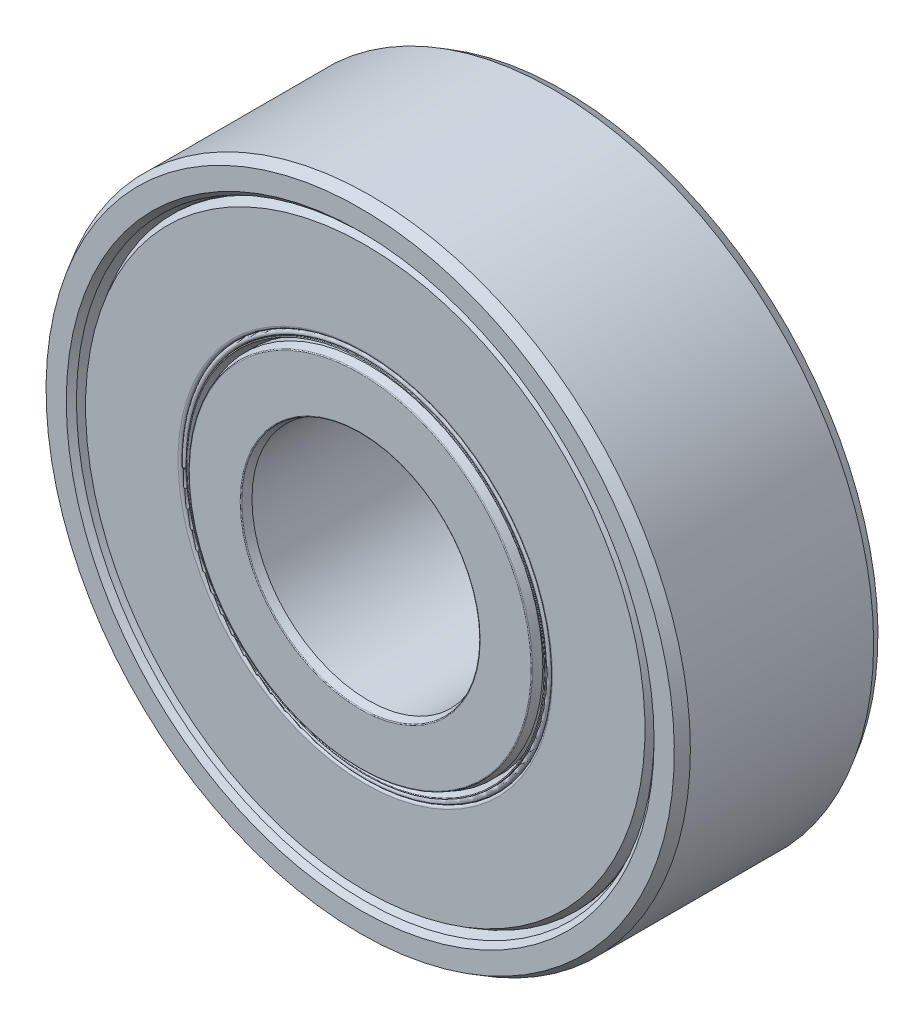
SolidWorks part; units mm, degrees
ref_plane "Front Plane" through (0, 0, 0) normal (0, 0, 1) x (1, 0, 0)
ref_plane "Top Plane" through (0, 0, 0) normal (0, 1, 0) x (1, 0, 0)
ref_plane "Right Plane" through (0, 0, 0) normal (1, 0, 0) x (0, 0, -1)
sketch "Sketch1" plane through (0, 0, 0) normal (0, 0, 1) x (1, 0, 0)
  line L0 (-11, 0) -> (11, 0) construction
  line L1 (-4, 0) -> (4, 0) construction
  circle A0 centre (0, 0) radius 4 construction
  circle A1 centre (0, 0) radius 11 construction
  point P3 (0, 0)
  point P6 (0, 0)
  point P7 (0, -4)
  point P11 (0, -11)
  point P12 (0, 4)
  point P13 (0, 11)
  dimension "OD" = 22
  dimension "ID" = 8
sketch "Sketch2" plane through (0, 0, 0) normal (1, 0, 0) x (0, 0, -1)
  line L0 (-3.5, 11) -> (3.5, 11) construction
  line L1 (0, 11) -> (0, -11) construction
  line L2 (3.15, 11) -> (-3.15, 11)
  line L3 (-3.15, 11) -> (-3.5, 10.7979)
  line L4 (-3.5, 10.7979) -> (-3.5, 10.1032)
  line L5 (-2.9452, 9.79) -> (-1.631, 9.79)
  line L6 (2.9452, 9.79) -> (1.631, 9.79)
  line L7 (3.5, 10.7979) -> (3.5, 10.1032)
  line L8 (3.15, 11) -> (3.5, 10.7979)
  line L9 (-1.631, 9.79) -> (-1.631, 11) construction
  line L10 (-1.631, 10.395) -> (0, 10.395) construction
  line L11 (0, 11) -> (0, -11) construction
  line L12 (-3.5, 0) -> (3.5, 0) construction
  line L13 (3.5, 4) -> (-3.5, 4) construction
  line L14 (-3.5, 4) -> (-3.5, -4) construction
  line L15 (-3.5, -4) -> (3.5, -4) construction
  line L16 (3.5, 11) -> (3.5, -11) construction
  line L20 (-2.9452, 9.79) -> (-3.325, 9.9282)
  line L21 (-3.325, 9.9282) -> (-3.5, 10.1032)
  line L26 (3.325, 9.9282) -> (3.5, 10.1032)
  line L27 (2.9452, 9.79) -> (3.325, 9.9282)
  arc A0 (-1.631, 9.79) -> (1.631, 9.79) centre (0, 7.894) cw
  circle A1 centre (0, 7.894) radius 2.501 construction
  point P17 (0, 0)
  point P21 (0, 11)
  point P30 (0, -4)
  dimension "Width" = 7
  dimension "D3" = 3.262
  dimension "For Shaft Diameter" = 8
  dimension "For Housing ID" = 22
  dimension "D4" = 19.58
  dimension "D2" = 20
  dimension "D5" = 45
  dimension "D1" = 30
  dimension "D6" = 0.35
  dimension "D7" = 0.175
sketch "Sketch3" plane through (0, 0, 0) normal (1, 0, 0) x (0, 0, -1)
  line L14 (-2.9452, 9.79) -> (-3.325, 9.9282) construction
  line L15 (-3.325, 9.9282) -> (-3.5, 10.1032) construction
  line L16 (-3.5, 10.7979) -> (-3.5, 10.1032) construction
  line L17 (-3.15, 11) -> (-3.5, 10.7979) construction
  line L18 (3.15, 11) -> (-3.15, 11) construction
  line L19 (3.15, 11) -> (3.5, 10.7979) construction
  line L20 (3.5, 10.7979) -> (3.5, 10.1032) construction
  line L21 (3.325, 9.9282) -> (3.5, 10.1032) construction
  line L22 (2.9452, 9.79) -> (3.325, 9.9282) construction
  line L23 (2.9452, 9.79) -> (1.631, 9.79) construction
  line L24 (-2.9452, 9.79) -> (-1.631, 9.79) construction
  line L25 (-2.9452, 9.79) -> (-3.325, 9.9282)
  line L26 (-3.325, 9.9282) -> (-3.5, 10.1032)
  line L27 (-3.5, 10.7979) -> (-3.5, 10.1032)
  line L28 (-3.15, 11) -> (-3.5, 10.7979)
  line L29 (3.15, 11) -> (-3.15, 11)
  line L30 (3.15, 11) -> (3.5, 10.7979)
  line L31 (3.5, 10.7979) -> (3.5, 10.1032)
  line L32 (3.325, 9.9282) -> (3.5, 10.1032)
  line L33 (2.9452, 9.79) -> (3.325, 9.9282)
  line L34 (2.9452, 9.79) -> (1.631, 9.79)
  line L35 (-2.9452, 9.79) -> (-1.631, 9.79)
  arc A2 (1.631, 9.79) -> (-1.631, 9.79) centre (0, 7.894) ccw construction
  arc A3 (1.631, 9.79) -> (-1.631, 9.79) centre (0, 7.894) ccw
revolve "Revolve1" add sketch "Sketch3" angle 360 about L12
sketch "Sketch4" plane through (0, 0, 0) normal (1, 0, 0) x (0, 0, -1)
  line L0 (0, 11) -> (0, -11) construction
  line L1 (0, 11) -> (0, -11) construction
  line L2 (-3.22, 4) -> (-3.477, 4.0935)
  line L3 (-3.5, 4.1264) -> (-3.5, 5.8716)
  line L4 (3.22, 5.998) -> (3.477, 5.9045)
  line L5 (-3.22, 5.998) -> (-1.631, 5.998)
  line L6 (-3.22, 4) -> (3.22, 4)
  line L7 (3.5, 10.7979) -> (3.5, 10.1032) construction
  line L8 (3.22, 4) -> (3.477, 4.0935)
  line L9 (1.631, 5.998) -> (1.631, 4) construction
  line L10 (3.5, 4.1264) -> (3.5, 5.8716)
  line L11 (3.22, 5.998) -> (1.631, 5.998)
  line L12 (-3.22, 5.998) -> (-3.477, 5.9045)
  line L14 (1.631, 4.999) -> (3.5, 4.999) construction
  circle A0 centre (0, 7.894) radius 2.501 construction
  arc A1 (1.631, 5.998) -> (-1.631, 5.998) centre (0, 7.894) cw
  arc A2 (3.477, 5.9045) -> (3.5, 5.8716) centre (3.465, 5.8716) cw
  arc A3 (-3.477, 5.9045) -> (-3.5, 5.8716) centre (-3.465, 5.8716) ccw
  arc A4 (3.477, 4.0935) -> (3.5, 4.1264) centre (3.465, 4.1264) ccw
  arc A5 (-3.477, 4.0935) -> (-3.5, 4.1264) centre (-3.465, 4.1264) cw
  point P14 (3.5, 4.1019)
  dimension "D2" = 0.035
  dimension "D1" = 20
  dimension "D3" = 0.28
revolve "Revolve2" add sketch "Sketch4" angle 360 about L12
sketch "Sketch5" plane through (0, 0, 0) normal (1, 0, 0) x (0, 0, -1)
  line L0 (-2.501, 7.894) -> (2.501, 7.894)
  arc A2 (-2.501, 7.894) -> (2.501, 7.894) centre (0, 7.894) cw
  arc A3 (1.631, 9.79) -> (-1.631, 9.79) centre (0, 7.894) ccw construction
revolve "Revolve3" add sketch "Sketch5" angle 360 about L0
pattern_circular "CirPattern1" count 7 over 360 about axis through (0, 0, 0) along (0, 0, 1) of bodies 104
sketch "Sketch6" plane through (0, 0, 0) normal (1, 0, 0) x (0, 0, -1)
  line L1 (-3.0219, 9.79) -> (-2.501, 9.79)
  line L2 (-3.325, 9.615) -> (-3.325, 6.4355)
  line L3 (-3.2375, 6.348) -> (-2.501, 6.348)
  line L4 (-2.501, 9.79) -> (-2.501, 6.348)
  line L6 (-3.15, 11) -> (-3.5, 10.7979) construction
  line L7 (0, 11) -> (0, 4) construction
  line L8 (3.2375, 6.348) -> (2.501, 6.348)
  line L9 (2.501, 9.79) -> (2.501, 6.348)
  line L10 (3.0219, 9.79) -> (2.501, 9.79)
  line L11 (3.325, 9.615) -> (3.325, 6.4355)
  line L13 (-3.22, 5.998) -> (-1.631, 5.998) construction
  line L14 (-3.325, 9.615) -> (-3.0219, 9.79)
  line L15 (-2.9452, 9.79) -> (-1.631, 9.79) construction
  line L16 (3.325, 9.615) -> (3.0219, 9.79)
  arc A0 (-3.325, 6.4355) -> (-3.2375, 6.348) centre (-3.2375, 6.4355) ccw
  circle A1 centre (0, 7.894) radius 2.501 construction
  arc A2 (3.325, 6.4355) -> (3.2375, 6.348) centre (3.2375, 6.4355) cw
  point P10 (-3.325, 10.899)
  point P26 (-3.325, 6.348)
  dimension "D3" = 0.0875
  dimension "D1" = 0.35
  dimension "D2" = 0.175
revolve "Revolve4" add sketch "Sketch6" angle 360 about L12
sketch "Sketch7" plane through (0, 0, 0) normal (1, 0, 0) x (0, 0, -1)
  line L0 (-2.501, 5.998) -> (-2.9259, 5.998)
  line L5 (-2.9259, 5.998) -> (-3.3135, 6.1391)
  line L6 (-3.3075, 6.173) -> (-3.2375, 6.173)
  line L7 (0, 5.393) -> (0, 4) construction
  line L8 (0, 11) -> (0, -11) construction
  line L9 (-3.2375, 6.348) -> (-2.501, 6.348)
  line L12 (-2.501, 6.348) -> (-2.501, 5.998)
  line L13 (-3.22, 5.998) -> (-1.631, 5.998) construction
  line L14 (-3.2375, 6.348) -> (-2.501, 6.348) construction
  line L15 (-2.501, 9.79) -> (-2.501, 6.348) construction
  line L16 (2.501, 6.348) -> (2.501, 5.998)
  line L17 (3.2375, 6.348) -> (2.501, 6.348)
  line L18 (3.3075, 6.173) -> (3.2375, 6.173)
  line L19 (2.9259, 5.998) -> (3.3135, 6.1391)
  line L20 (2.501, 5.998) -> (2.9259, 5.998)
  circle A2 centre (0, 7.894) radius 2.501 construction
  arc A5 (-3.3135, 6.1391) -> (-3.3075, 6.173) centre (-3.3075, 6.1555) cw
  arc A6 (-3.2375, 6.173) -> (-3.2375, 6.348) centre (-3.2375, 6.2605) cw
  arc A7 (3.2375, 6.173) -> (3.2375, 6.348) centre (3.2375, 6.2605) ccw
  arc A8 (3.3135, 6.1391) -> (3.3075, 6.173) centre (3.3075, 6.1555) ccw
  point P14 (-3.325, 6.2605)
  point P27 (-2.501, 6.173)
  point P36 (-3.325, 6.1555)
  dimension "D1" = 20
  dimension "D2" = 0.0175
revolve "Revolve5" add sketch "Sketch7" angle 360 about L12
equation "\"D3@Sketch2\"=\"Width@Sketch2\" *.466"
equation "\"D4@Sketch2\"=\"OD@Sketch1\"*.89"
equation "\"D1@Sketch6\"=(\"OD@Sketch1\"-\"ID@Sketch1\")*.025"
equation "\"D2@Sketch6\"=\"D1@Sketch6\"*.5"
equation "\"D3@Sketch6\"=\"D1@Sketch6\"*.25"
equation "\"D3@Sketch4\"=\"Width@Sketch2\"*.04"
equation "\"D2@Sketch4\"=\"D3@Sketch4\"*.125"
equation "\"D6@Sketch2\"=\"Width@Sketch2\"*.05"
equation "\"D7@Sketch2\"=\"D6@Sketch2\"*.5"
equation "\"D2@Sketch7\"=\"D6@Sketch2\"*.05"
